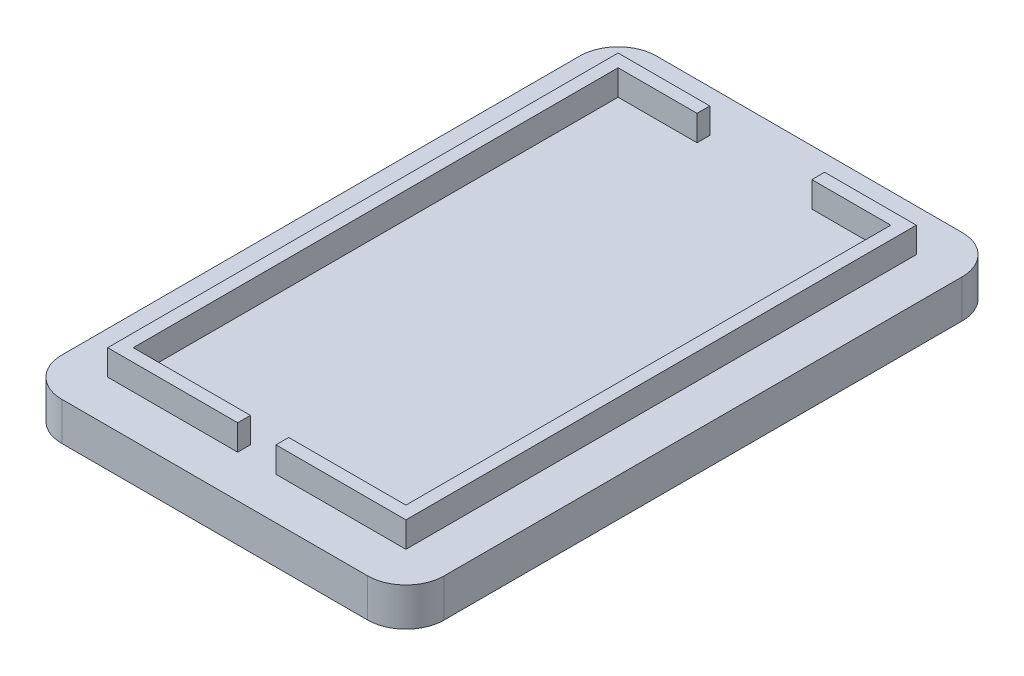
SolidWorks part; units mm, degrees
ref_plane "Front Plane" through (0, 0, 0) normal (0, 0, 1) x (1, 0, 0)
ref_plane "Top Plane" through (0, 0, 0) normal (0, 1, 0) x (1, 0, 0)
ref_plane "Right Plane" through (0, 0, 0) normal (1, 0, 0) x (0, 0, -1)
sketch "Sketch1" plane through (0, 0, 0) normal (0, 1, 0) x (1, 0, 0)
  line L0 (-14.985, 23.3) -> (-14.985, -23.3)
  line L1 (-11.985, 20.3) -> (11.985, 20.3) construction
  line L2 (-11.985, 20.3) -> (-11.985, -20.3) construction
  line L3 (-11.985, -20.3) -> (11.985, -20.3) construction
  line L4 (11.985, 20.3) -> (11.985, -20.3) construction
  line L5 (-11.985, 20.3) -> (11.985, -20.3) construction
  line L6 (-11.985, -20.3) -> (11.985, 20.3) construction
  line L7 (-14.985, -23.3) -> (14.985, -23.3)
  line L8 (14.985, 23.3) -> (14.985, -23.3)
  line L9 (-14.985, 23.3) -> (14.985, 23.3)
  point P0 (0, 0)
  dimension "D2" = 40.6
  dimension "D3" = 23.97
  dimension "D1" = 3
extrude "Boss-Extrude1" add sketch "Sketch1" along normal blind 3 contours L2 L1 L4 L3
sketch "Sketch2" plane through (0, 3, 0) normal (0, 1, 0) x (1, 0, 0)
  line L4 (11.685, 20) -> (-11.685, 20)
  line L5 (-11.685, 20) -> (-11.685, -20)
  line L6 (-11.685, -20) -> (11.685, -20)
  line L7 (11.685, -20) -> (11.685, 20)
  line L8 (11.985, 20.3) -> (-11.985, 20.3)
  line L9 (-11.985, 20.3) -> (-11.985, -20.3)
  line L10 (-11.985, -20.3) -> (11.985, -20.3)
  line L11 (11.985, -20.3) -> (11.985, 20.3)
  line L12 (11.985, 20.3) -> (-11.985, 20.3) construction
  line L13 (-11.985, 20.3) -> (-11.985, -20.3) construction
  line L14 (-11.985, -20.3) -> (11.985, -20.3) construction
  line L15 (11.985, -20.3) -> (11.985, 20.3) construction
  line L16 (10.685, 19) -> (-10.685, 19)
  line L17 (-10.685, 19) -> (-10.685, -19)
  line L18 (-10.685, -19) -> (10.685, -19)
  line L19 (10.685, -19) -> (10.685, 19)
  line L20 (0, 23.3) -> (0, 20.3) construction
  line L21 (-4.5, 20) -> (4.5, 20)
  line L22 (-4.5, 20) -> (-4.5, 19)
  line L23 (-4.5, 19) -> (4.5, 19)
  line L24 (4.5, 20) -> (4.5, 19)
  line L25 (14.985, 23.3) -> (-14.985, 23.3) construction
  line L27 (-1.5, -19) -> (1.5, -19)
  line L28 (-1.5, -19) -> (-1.5, -20)
  line L29 (-1.5, -20) -> (1.5, -20)
  line L30 (1.5, -19) -> (1.5, -20)
  point P20 (0, 0)
  dimension "D4" = 9
  dimension "D5" = 3
  dimension "D1" = 3
  dimension "D2" = 0.3
  dimension "D3" = 1
extrude "Boss-Extrude2" add sketch "Sketch2" along normal blind 2 contours L28 L18 L17 L16 L22 L4 L5 L6 | L18 L30 L6 L7 L4 L24 L16 L19
fillet "Fillet1" radius 3 4 edges at (14.985, 1.5, -23.3) (14.985, 1.5, 23.3) (-14.985, 1.5, 23.3) (-14.985, 1.5, -23.3)
